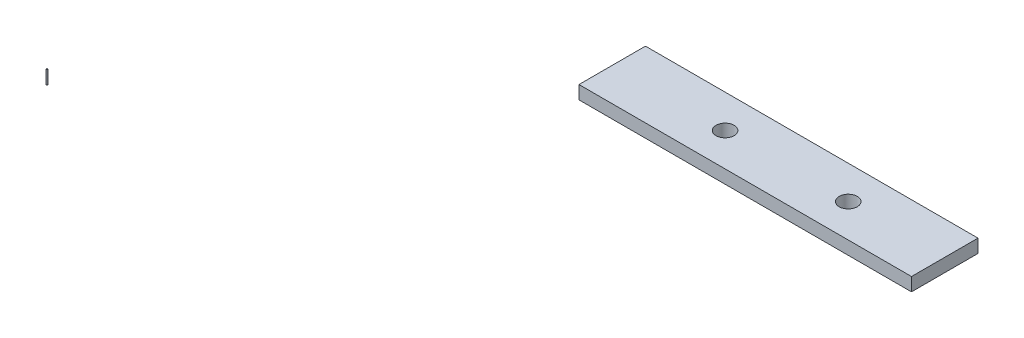
SolidWorks part; units mm, degrees
ref_plane "Front Plane" through (0, 0, 0) normal (0, 0, 1) x (1, 0, 0)
ref_plane "Top Plane" through (0, 0, 0) normal (0, 1, 0) x (1, 0, 0)
ref_plane "Right Plane" through (0, 0, 0) normal (1, 0, 0) x (0, 0, -1)
sketch "Sketch1" plane through (0, 0, 0) normal (0, 1, 0) x (1, 0, 0)
  line L1 (0, 0) -> (107.95, 0)
  line L2 (0, 0) -> (0, 58.42)
  line L3 (0, 58.42) -> (107.95, 58.42)
  line L4 (107.95, 0) -> (107.95, 58.42)
  dimension "D1" = 107.95
  dimension "D2" = 58.42
extrude "Boss-Extrude1" add sketch "Sketch1" along normal blind 2.54
ref_plane "Plane1" through (107.95, 2.54, -58.42) normal (0, 0, -1) x (-1, 0, 0)
sketch "Sketch3" plane through (0, 2.54, 0) normal (0, 1, 0) x (1, 0, 0)
  line L0 (0, 35.56) -> (63.5, 35.56)
  line L1 (63.5, 35.56) -> (63.5, 22.86)
  line L2 (63.5, 22.86) -> (0, 22.86)
  line L3 (0, 29.21) -> (107.95, 29.21) construction
  line L4 (0, 58.42) -> (0, 0)
  line L5 (0, 0) -> (107.95, 0)
  line L6 (107.95, 0) -> (107.95, 58.42)
  line L7 (107.95, 58.42) -> (0, 58.42)
  line L8 (0, 35.56) -> (0, 22.86)
  point P6 (0, 29.21)
  dimension "D2" = 12.7
  dimension "D3" = 63.5
  dimension "D1" = 0
extrude "Cut-Extrude1" cut sketch "Sketch3" against normal blind 2.54 flip side to cut
sketch "Sketch4" plane through (0, 2.54, 0) normal (0, 1, 0) x (-1, 0, 0)
  line L0 (-38.824, -33.8833) -> (-51.306, -33.8833) construction
  line L1 (-38.824, -34.671) -> (-38.824, -30.607) construction
  line L2 (-51.306, -34.7723) -> (-51.306, -32.9943) construction
  line L3 (-45.065, -35.56) -> (-45.065, -22.86) construction
  line L4 (0, -22.86) -> (-63.5, -22.86) construction
  line L5 (-63.5, -35.56) -> (0, -35.56) construction
  line L6 (0, -29.21) -> (-107.95, -29.21) construction
  line L7 (-27.9, -32.9943) -> (-27.9, -30.96) construction
  line L10 (-15.2, -30.96) -> (-27.9, -30.96) construction
  line L11 (-21.55, -35.56) -> (-21.55, -22.86) construction
  circle A0 centre (-45.065, -29.21) radius 1.7272
  circle A1 centre (-21.55, -29.21) radius 1.7272
  point P6 (-45.065, -33.8833)
  point P20 (-21.55, -30.96)
  dimension "D1" = 3.4544
extrude "Cut-Extrude2" cut sketch "Sketch4" against normal blind 2.54
sketch "Sketch5" plane through (0, 2.54, 0) normal (0, 1, 0) x (1, 0, 0)
  line L0 (0, 22.86) -> (-50.8, 22.86) construction
  line L1 (-50.8, 22.86) -> (-50.8, -27.94) construction
  circle A0 centre (-50.8, -27.94) radius 0.127
  dimension "D3" = 0.254
  dimension "D1" = 50.8
  dimension "D2" = 50.8
extrude "Boss-Extrude2" add sketch "Sketch5" along normal blind 2.54 separate body
